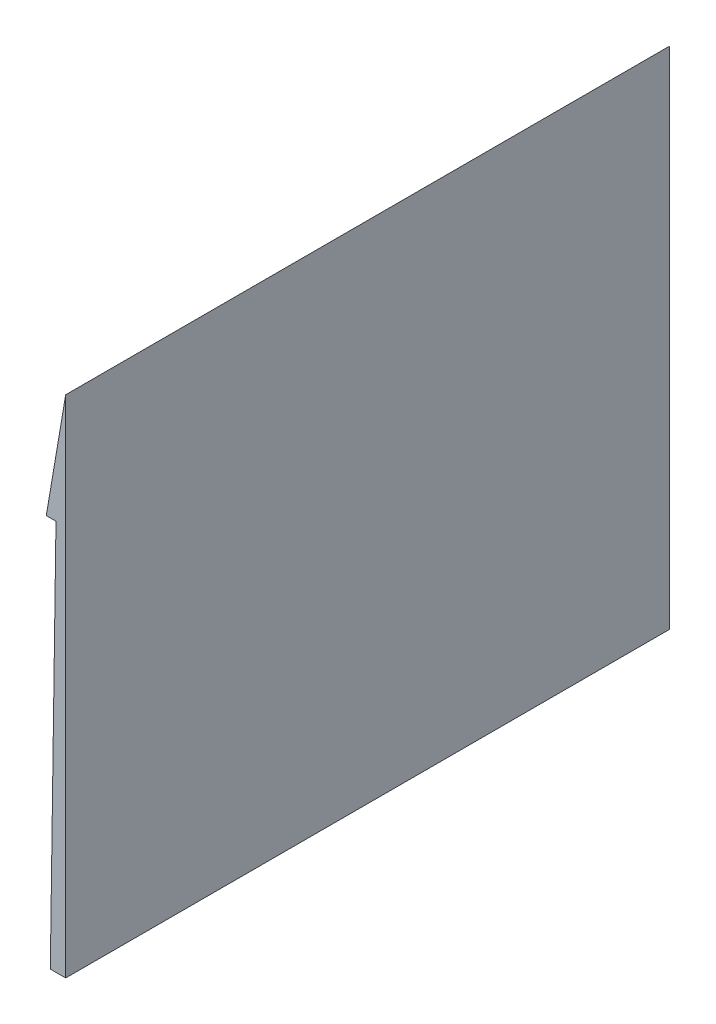
SolidWorks part; units mm, degrees
ref_plane "Front" through (0, 0, 0) normal (0, 0, 1) x (1, 0, 0)
ref_plane "Top" through (0, 0, 0) normal (0, 1, 0) x (1, 0, 0)
ref_plane "Right" through (0, 0, 0) normal (1, 0, 0) x (0, 0, -1)
sketch "Sketch1" plane through (0, 0, 0) normal (0, 0, 1) x (1, 0, 0)
  line L0 (0, 7.2887) -> (0, 26.2287)
  line L1 (0, 26.2287) -> (-3.2152, 7.2887)
  line L3 (0, 26.2287) -> (0, 7.2887) construction
  line L5 (0, 7.2887) -> (0, -57.396)
  line L6 (0, -57.396) -> (-2.5484, -57.396)
  line L7 (-2.5484, -57.396) -> (-1.6076, 7.2887)
  line L9 (-3.2152, 7.2887) -> (-1.6076, 7.2887)
  point P0 (0, -57.396)
  dimension "D3" = 18.94
extrude "Boss-Extrude1" add sketch "Sketch1" along normal mid plane 100
ref_plane "Plane3" through (10, 0, 0) normal (1, 0, 0) x (0, 0, -1)
sketch "Sketch4" plane through (10, 0, 0) normal (1, 0, 0) x (0, 0, -1)
  line L1 (44.6622, -20.3904) -> (44.6622, 6.8988)
  line L3 (17.8385, 6.8988) -> (17.8385, 18.605) construction
  line L4 (-42.0898, 6.8988) -> (44.6622, 6.8988)
  line L6 (-42.0898, 6.8988) -> (-36.8973, -15.1384) construction
  line L7 (-36.8973, -15.1384) -> (-33.1419, -29.2321) construction
  line L8 (-33.1419, -29.2321) -> (-33.1419, -37.945) construction
  line L9 (-33.1419, -37.945) -> (32.6254, -37.945)
  arc A0 (32.6254, -37.945) -> (44.6622, -20.3904) centre (50.5025, -37.2989) cw
  spline S1 degree 3 poles (-42.0898, 6.8988) (-36.8973, -15.1384) (-33.1419, -29.2321) (-33.1419, -37.945) knots 0 0 0 0 1 1 1 1
  dimension "D4" = 17.8888
  dimension "D8" = 44.6622
  dimension "D1" = 21.2849
  dimension "D7" = 65.7673
sketch "Sketch5" plane through (0, 0, 0) normal (1, 0, 0) x (0, 0, -1)
  line L0 (-42.0898, 6.8988) -> (44.6622, 6.8988) construction
  line L1 (44.6622, -20.3904) -> (44.6622, 6.8988) construction
  line L2 (-33.1419, -37.945) -> (32.6254, -37.945) construction
  line L3 (-42.0898, 6.8988) -> (44.6622, 6.8988)
  line L4 (50, -57.396) -> (50, 26.2287)
  line L5 (50, 26.2287) -> (-50, 26.2287)
  line L6 (-50, 26.2287) -> (-50, -57.396)
  line L7 (-50, -57.396) -> (50, -57.396)
  line L8 (50, -57.396) -> (50, 26.2287)
  line L9 (50, 26.2287) -> (-50, 26.2287)
  line L10 (-50, 26.2287) -> (-50, -57.396)
  line L11 (-50, -57.396) -> (50, -57.396)
  line L12 (44.6622, -20.3904) -> (44.6622, 6.8988)
  line L13 (-33.1419, -37.945) -> (32.6254, -37.945)
  line L15 (-50, 6.8988) -> (-50, -37.945)
  line L18 (50, 6.8988) -> (50, -20.3904)
  arc A0 (44.6622, -20.3904) -> (32.6254, -37.945) centre (50.5025, -37.2989) ccw construction
  arc A1 (44.6622, -20.3904) -> (32.6254, -37.945) centre (50.5025, -37.2989) ccw
  spline S0 degree 3 poles (575.7713, 2922.1072) (-1267.4416, -2153.4929) (1939.1645, 1372.0882) (-2871.7627, -945.8596) knots -7.497468 -7.497468 -7.497468 -7.497468 10.299432 10.299432 10.299432 10.299432 only from (-42.0898, 6.8988) to (-33.1419, -37.945) construction
  spline S1 degree 3 poles (-42.0898, 6.8988) (-36.8973, -15.1384) (-33.1419, -29.2321) (-33.1419, -37.945) knots 0 0 0 0 1 1 1 1
  point P10 (0, 0)
  point P15 (0, 0)
  point P16 (44.6622, -20.3904)
  dimension "D1" = 0
